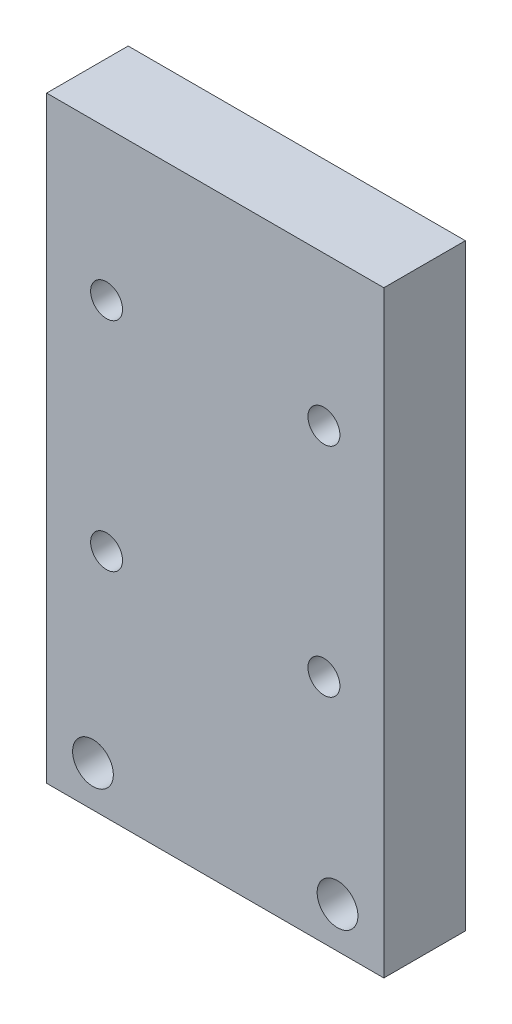
SolidWorks part; units mm, degrees
ref_plane "Plan de face" through (0, 0, 0) normal (0, 0, 1) x (1, 0, 0)
ref_plane "Plan de dessus" through (0, 0, 0) normal (0, 1, 0) x (1, 0, 0)
ref_plane "Plan de droite" through (0, 0, 0) normal (1, 0, 0) x (0, 0, -1)
sketch "Esquisse1" plane through (0, 0, 0) normal (0, 0, 1) x (1, 0, 0)
  line L1 (-64.0159, 42.1859) -> (-39.1959, 42.1859)
  line L2 (-64.0159, 42.1859) -> (-64.0159, -1.8141)
  line L3 (-64.0159, -1.8141) -> (-39.1959, -1.8141)
  line L4 (-39.1959, 42.1859) -> (-39.1959, -1.8141)
  circle A0 centre (-60.6059, 1.1859) radius 1.5
  circle A1 centre (-42.6059, 1.1859) radius 1.5
  dimension "D3" = 3
  dimension "D4" = 3
  dimension "D1" = 44
  dimension "D2" = 24.82
  dimension "D5" = 18
  dimension "D6" = 3.41
  dimension "D7" = 3
extrude "Boss.-Extru.1" add sketch "Esquisse1" along normal blind 6
sketch "Esquisse2" plane through (0, 0, 6) normal (0, 0, 1) x (1, 0, 0)
  line L0 (-39.1959, -1.8141) -> (-39.1959, 42.1859) construction
  line L2 (-39.1959, 42.1859) -> (-64.0159, 42.1859) construction
  circle A0 centre (-43.6059, 31.1859) radius 1.175
  circle A1 centre (-59.6059, 31.1859) radius 1.175
  circle A2 centre (-59.6059, 15.1859) radius 1.175
  circle A3 centre (-43.6059, 15.1859) radius 1.175
  dimension "D7" = 2.35
  dimension "D8" = 2.35
  dimension "D9" = 2.35
  dimension "D10" = 2.35
  dimension "D1" = 4.41
  dimension "D2" = 4.41
  dimension "D3" = 16
  dimension "D4" = 16
  dimension "D5" = 16
  dimension "D6" = 16
  dimension "D11" = 11
  dimension "D12" = 11
extrude "Enlèv. mat.-Extru.1" cut sketch "Esquisse2" against normal blind 6
